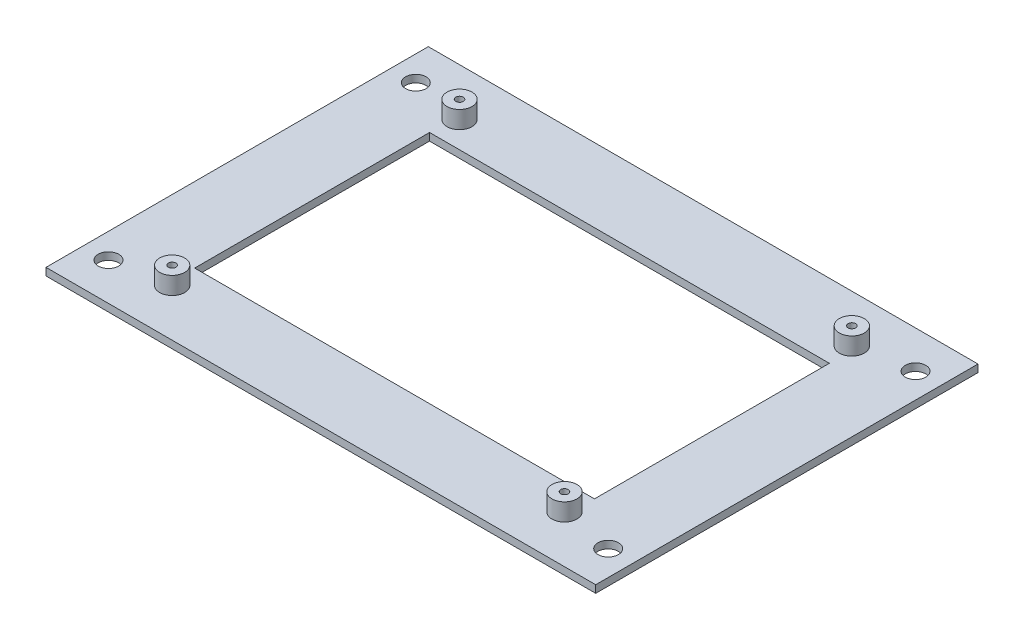
SolidWorks part; units mm, degrees
ref_plane "Front" through (0, 0, 0) normal (0, 0, 1) x (1, 0, 0)
ref_plane "Top" through (0, 0, 0) normal (0, 1, 0) x (1, 0, 0)
ref_plane "Right" through (0, 0, 0) normal (1, 0, 0) x (0, 0, -1)
sketch "Croquis1" plane through (0, 0, 0) normal (0, 1, 0) x (1, 0, 0)
  line L1 (-110, 76.5) -> (110, 76.5)
  line L2 (-110, 76.5) -> (-110, -76.5)
  line L3 (-110, -76.5) -> (110, -76.5)
  line L4 (110, 76.5) -> (110, -76.5)
  line L5 (-110, 76.5) -> (110, -76.5) construction
  line L6 (-110, -76.5) -> (110, 76.5) construction
  point P0 (0, 0)
  dimension "D1" = 153
  dimension "D2" = 220
extrude "Saliente-Extruir1" add sketch "Croquis1" along normal blind 3
sketch "Croquis2" plane through (0, 3, 0) normal (0, 1, 0) x (1, 0, 0)
  line L0 (0, 0) -> (0, 50000) construction
  line L2 (-80, 47) -> (80, 47)
  line L3 (-80, 47) -> (-80, -47)
  line L4 (-80, -47) -> (80, -47)
  line L5 (80, 47) -> (80, -47)
  line L6 (-80, 47) -> (80, -47) construction
  line L7 (-80, -47) -> (80, 47) construction
  point P3 (0, 0)
  point P8 (0, 0)
  dimension "D1" = 160
  dimension "D2" = 94
extrude "Cortar-Extruir1" cut sketch "Croquis2" against normal through all
sketch "Croquis3" plane through (0, 3, 0) normal (0, 1, 0) x (1, 0, 0)
  line L0 (110, 76.5) -> (-110, 76.5) construction
  line L1 (-110, 76.5) -> (-110, -76.5) construction
  circle A0 centre (-100, 61.5) radius 4.1
  point P2 (0, 0)
  dimension "D1" = 8.2
  dimension "D2" = 15
  dimension "D3" = 10
extrude "Cortar-Extruir2" cut sketch "Croquis3" against normal through all
sketch "Croquis4" plane through (0, 3, 0) normal (0, 1, 0) x (1, 0, 0)
  circle A0 centre (-78.5, 57.5) radius 5
  dimension "D1" = 10
extrude "Saliente-Extruir2" add sketch "Croquis4" along normal blind 7
sketch "Croquis5" plane through (0, 10, 0) normal (0, 1, 0) x (1, 0, 0)
  circle A1 centre (-78.5, 57.5) radius 1.5
extrude "Cortar-Extruir3" cut sketch "Croquis5" against normal through all
sketch "Croquis6" plane through (0, 0, 0) normal (0, -1, 0) x (1, 0, 0)
  line L1 (-81.6754, -57.5) -> (-80.0877, -60.25)
  line L2 (-80.0877, -60.25) -> (-76.9123, -60.25)
  line L3 (-76.9123, -60.25) -> (-75.3246, -57.5)
  line L4 (-75.3246, -57.5) -> (-76.9123, -54.75)
  line L5 (-76.9123, -54.75) -> (-80.0877, -54.75)
  line L6 (-80.0877, -54.75) -> (-81.6754, -57.5)
  circle A0 centre (-78.5, -57.5) radius 2.75 construction
  dimension "D1" = 5.5
extrude "Cortar-Extruir4" cut sketch "Croquis6" against normal blind 3
mirror "Simetría1" about plane through (0, 0, 0) normal (1, 0, 0) of "Cortar-Extruir3", "Cortar-Extruir2", "Saliente-Extruir2", "Cortar-Extruir4"
mirror "Simetría2" about plane through (0, 0, 0) normal (0, 0, 1) of "Simetría1", "Cortar-Extruir1", "Cortar-Extruir2"
